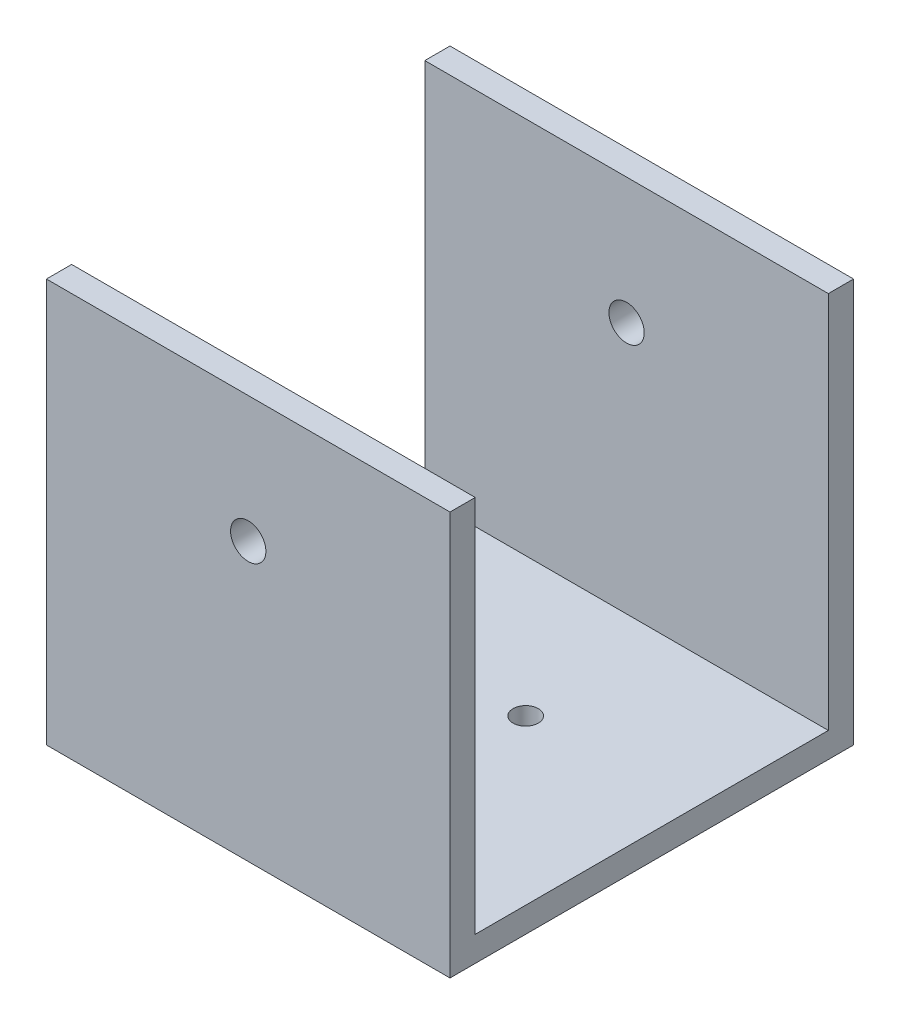
SolidWorks part; units mm, degrees
ref_plane "Front Plane" through (0, 0, 0) normal (0, 0, 1) x (1, 0, 0)
ref_plane "Top Plane" through (0, 0, 0) normal (0, 1, 0) x (1, 0, 0)
ref_plane "Right Plane" through (0, 0, 0) normal (1, 0, 0) x (0, 0, -1)
sketch "Sketch1" plane through (0, 0, 0) normal (0, 0, 1) x (1, 0, 0)
  line L1 (-40, 40) -> (40, 40)
  line L2 (-40, 40) -> (-40, -40)
  line L3 (-40, -40) -> (40, -40)
  line L4 (40, 40) -> (40, -40)
  line L5 (-40, 40) -> (40, -40) construction
  line L6 (-40, -40) -> (40, 40) construction
  circle A0 centre (0, 15) radius 3.5
  point P0 (-5.0386, 12.5833)
  point P8 (-1.5386, 6.4345)
  point P9 (-5.0386, 12.5833)
  point P10 (0, 0)
  dimension "D3" = 7
  dimension "D4" = 40
  dimension "D1" = 80
  dimension "D2" = 80
  dimension "D5" = 55
extrude "Boss-Extrude1" add sketch "Sketch1" along normal blind 80
sketch "Sketch2" plane through (40, 0, 0) normal (1, 0, 0) x (0, 0, -1)
  line L0 (-75, 40) -> (-75, -35)
  line L1 (-80, 40) -> (0, 40) construction
  line L2 (-75, -35) -> (-5, -35)
  line L3 (-5, -35) -> (-5, 40)
  line L4 (-5, 40) -> (-75, 40)
  line L5 (-80, -40) -> (-80, 40) construction
  line L6 (-80, -40) -> (0, -40) construction
  line L7 (0, -40) -> (0, 40) construction
  dimension "D1" = 5
  dimension "D2" = 5
  dimension "D3" = 5
extrude "Cut-Extrude1" cut sketch "Sketch2" against normal blind 80
sketch "Sketch3" plane through (0, -40, 0) normal (0, -1, 0) x (1, 0, 0)
  line L0 (-40, 80) -> (-40, 0) construction
  line L1 (-40, 80) -> (40, 80) construction
  line L2 (-27.5, 67.5) -> (7.5, 67.5) construction
  line L3 (-27.5, 67.5) -> (-27.5, 32.5) construction
  circle A0 centre (-27.5, 67.5) radius 2.5
  circle A1 centre (7.5, 67.5) radius 2.5
  circle A2 centre (7.5, 32.5) radius 2.5
  circle A3 centre (-27.5, 32.5) radius 2.5
  dimension "D1" = 5
  dimension "D2" = 12.5
  dimension "D3" = 12.5
  dimension "D6" = 35
  dimension "D7" = 35
  dimension "D4" = 2
  dimension "D5" = 2
extrude "Cut-Extrude2" cut sketch "Sketch3" against normal blind 60
